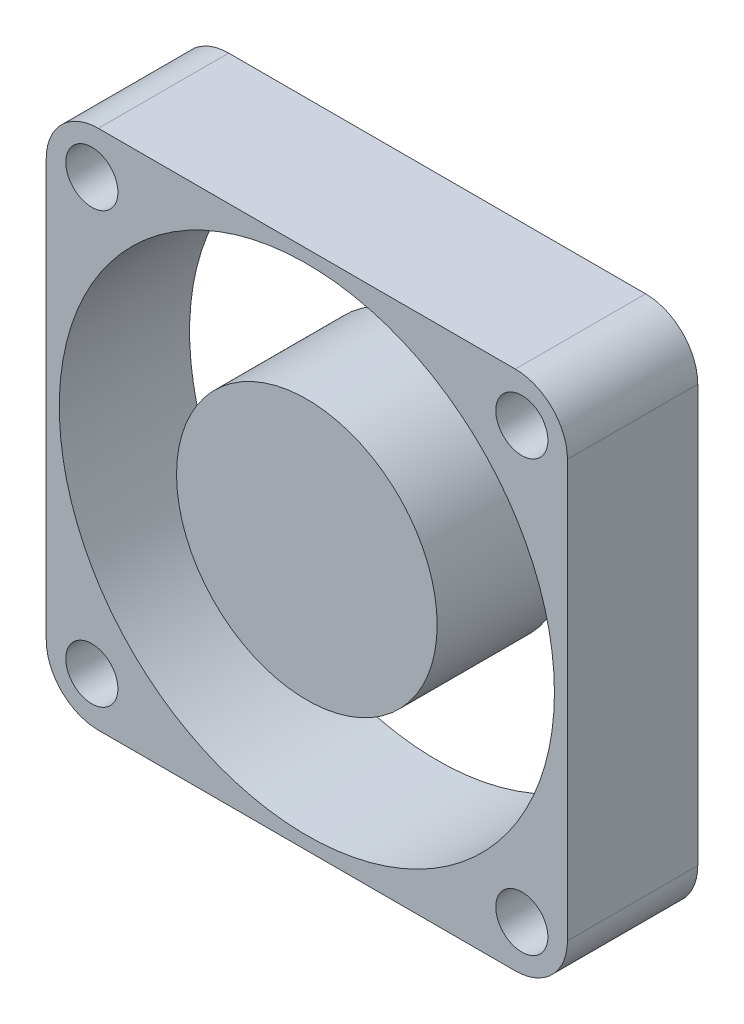
SolidWorks part; units mm, degrees
material "ABS"
ref_plane "Front Plane" through (0, 0, 0) normal (0, 0, 1) x (1, 0, 0)
ref_plane "Top Plane" through (0, 0, 0) normal (0, 1, 0) x (1, 0, 0)
ref_plane "Right Plane" through (0, 0, 0) normal (1, 0, 0) x (0, 0, -1)
sketch "Sketch1" plane through (0, 0, 0) normal (0, 0, 1) x (1, 0, 0)
  line L0 (40, 40) -> (0, 0) construction
  line L1 (0, 0) -> (40, 0)
  line L2 (0, 0) -> (0, 40)
  line L3 (0, 40) -> (40, 40)
  line L4 (40, 0) -> (40, 40)
  line L5 (3.5, 3.5) -> (36.5, 3.5) construction
  line L6 (3.5, 3.5) -> (3.5, 36.5) construction
  line L7 (3.5, 36.5) -> (36.5, 36.5) construction
  line L8 (36.5, 3.5) -> (36.5, 36.5) construction
  line L9 (0, 40) -> (40, 0) construction
  circle A0 centre (20, 20) radius 19
  circle A1 centre (36.5, 36.5) radius 2
  circle A2 centre (36.5, 3.5) radius 2
  circle A3 centre (3.5, 3.5) radius 2
  circle A4 centre (3.5, 36.5) radius 2
  circle A5 centre (20, 20) radius 10
  dimension "D4" = 38
  dimension "D5" = 4
  dimension "D6" = 20
  dimension "D1" = 40
  dimension "D2" = 3.5
  dimension "D3" = 3.5
extrude "Boss-Extrude1" add sketch "Sketch1" along normal blind 10 contours L1 L4 L3 L2 A4 A3 A2 A1 A0 | A5
fillet "Fillet1" radius 4 4 edges at (0, 40, 5) (0, 0, 5) (40, 0, 5) (40, 40, 5)
